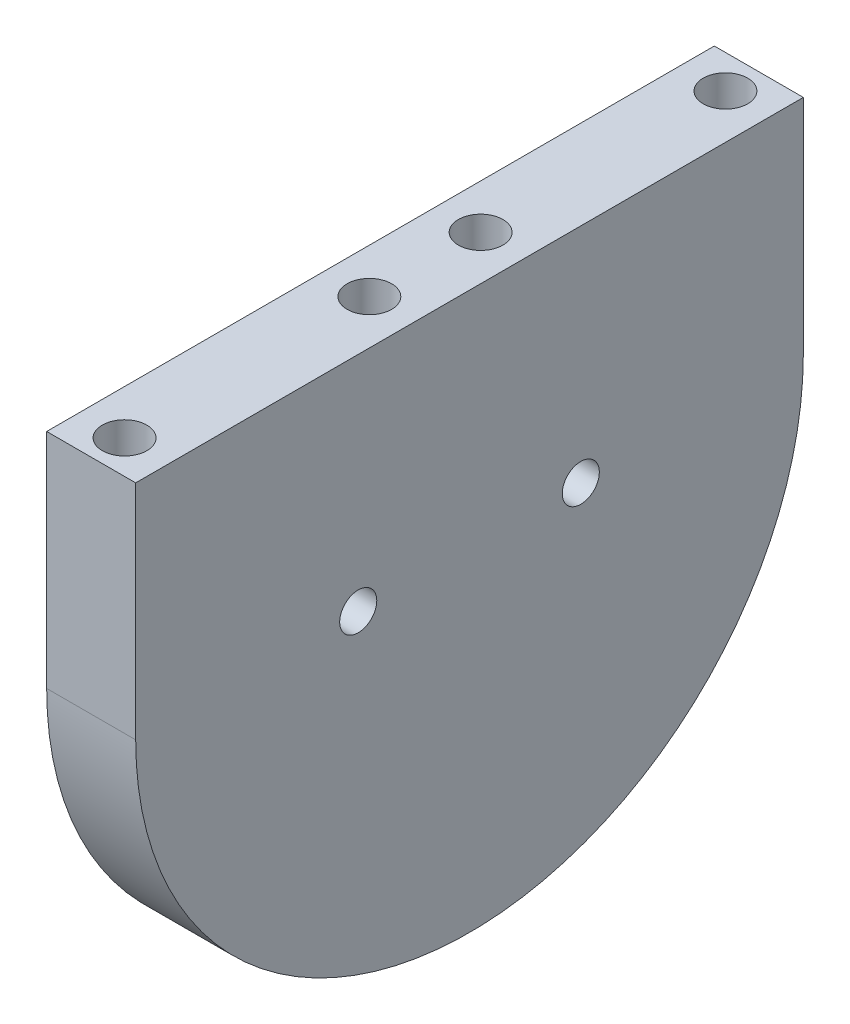
SolidWorks part; units mm, degrees
ref_plane "Front Plane" through (0, 0, 0) normal (0, 0, 1) x (1, 0, 0)
ref_plane "Top Plane" through (0, 0, 0) normal (0, 1, 0) x (1, 0, 0)
ref_plane "Right Plane" through (0, 0, 0) normal (1, 0, 0) x (0, 0, -1)
sketch "Sketch1" plane through (0, 0, 0) normal (1, 0, 0) x (0, 0, -1)
  line L0 (15, 0) -> (-15, 0) construction
  line L1 (-45, 0) -> (17.5, 0) construction
  line L6 (-45, 0) -> (-45, 30)
  line L7 (45, 0) -> (45, 30)
  line L8 (-45, 30) -> (45, 30)
  circle A0 centre (-15, 0) radius 2.5
  circle A1 centre (15, 0) radius 2.5
  arc A2 (-45, 0) -> (45, 0) centre (0, 0) ccw
  point P4 (0, 0)
  point P7 (0, 0)
  dimension "D1" = 5
  dimension "D3" = 45
  dimension "D2" = 30
  dimension "D4" = 30
extrude "Boss-Extrude1" add sketch "Sketch1" along normal blind 12
sketch "Sketch2" plane through (0, 30, 0) normal (0, 1, 0) x (1, 0, 0)
  line L0 (0, 0) -> (12, 0) construction
  line L1 (0, 45) -> (0, -45) construction
  line L2 (12, 45) -> (12, -45) construction
  line L3 (6, -7.5) -> (6, 7.5) construction
  line L4 (6, -40.5) -> (6, 40.5) construction
  circle A0 centre (6, 40.5) radius 3
  circle A1 centre (6, 7.5) radius 3
  circle A2 centre (6, -7.5) radius 3
  circle A3 centre (6, -40.5) radius 3
  point P9 (6, 0)
  point P12 (6, 0)
  dimension "D1" = 6
  dimension "D2" = 81
  dimension "D3" = 15
extrude "Cut-Extrude1" cut sketch "Sketch2" against normal blind 25
